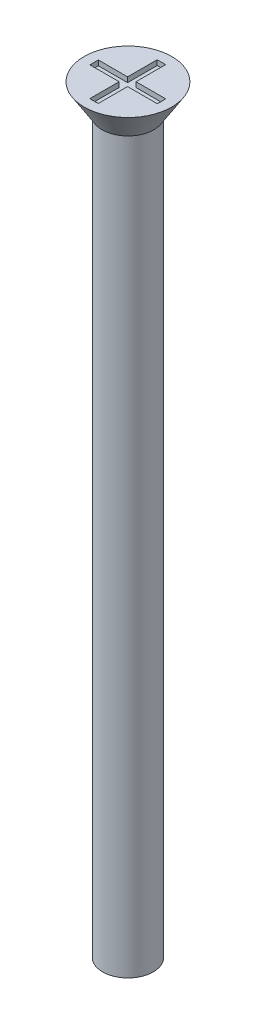
SolidWorks part; units mm, degrees
material "AISI 304"
ref_plane "Front" through (0, 0, 0) normal (0, 0, 1) x (1, 0, 0)
ref_plane "Top" through (0, 0, 0) normal (0, 1, 0) x (1, 0, 0)
ref_plane "Right" through (0, 0, 0) normal (1, 0, 0) x (0, 0, -1)
sketch "Sketch1" plane through (0, 0, 0) normal (0, 1, 0) x (1, 0, 0)
  circle A0 centre (0, 0) radius 1.5
  dimension "D1" = 3
extrude "Boss-Extrude1" add sketch "Sketch1" along normal blind 45
sketch "Sketch2" plane through (0, 45, 0) normal (0, 1, 0) x (1, 0, 0)
  circle A0 centre (0, 0) radius 2.6
  dimension "D1" = 5.2
extrude "Boss-Extrude2" add sketch "Sketch2" against normal blind 1.7 draft 32
sketch "Sketch3" plane through (0, 45, 0) normal (0, 1, 0) x (1, 0, 0)
  line L1 (-2, 0.2416) -> (2, 0.2416)
  line L2 (-2, 0.2416) -> (-2, -0.2584)
  line L3 (-2, -0.2584) -> (2, -0.2584)
  line L4 (2, 0.2416) -> (2, -0.2584)
  line L5 (-0.2653, 2) -> (0.2347, 2)
  line L6 (-0.2653, 2) -> (-0.2653, -2)
  line L7 (-0.2653, -2) -> (0.2347, -2)
  line L8 (0.2347, 2) -> (0.2347, -2)
  circle A0 centre (0, 0) radius 2.6 construction
  dimension "D1" = 0.5
  dimension "D2" = 0.5
  dimension "D3" = 4
  dimension "D4" = 4
  dimension "D5" = 2
  dimension "D6" = 2
extrude "Cut-Extrude1" cut sketch "Sketch3" against normal blind 0.3 contours L8 L5 L6 L1 | L8 L3 L6 L7 | L6 L1 L2 L3 | L1 L8 L3 L4 | L8 L1 L6 L3
